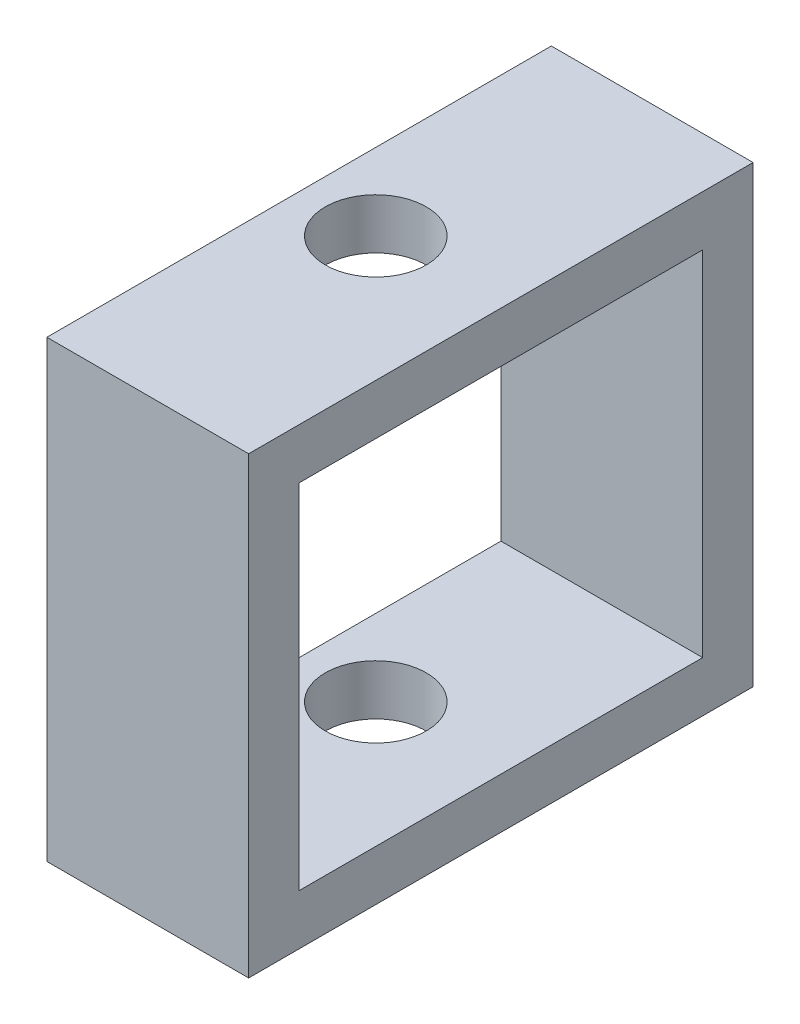
SolidWorks part; units mm, degrees
material "6061-T6 (SS)"
ref_plane "Front Plane" through (0, 0, 0) normal (0, 0, 1) x (1, 0, 0)
ref_plane "Top Plane" through (0, 0, 0) normal (0, 1, 0) x (1, 0, 0)
ref_plane "Right Plane" through (0, 0, 0) normal (1, 0, 0) x (0, 0, -1)
sketch "Sketch1" plane through (0, 0, 0) normal (0, 1, 0) x (1, 0, 0)
  line L1 (0, 0) -> (12.7, 0)
  line L2 (0, 0) -> (0, 31.75)
  line L3 (0, 31.75) -> (12.7, 31.75)
  line L4 (12.7, 0) -> (12.7, 31.75)
  circle A0 centre (4.826, 15.875) radius 3.175
  point P9 (0, 15.875)
  dimension "D1" = 6.35
  dimension "D2" = 31.75
  dimension "D3" = 12.7
  dimension "D5" = 4.826
extrude "Boss-Extrude2" add sketch "Sketch1" along normal blind 3.175
sketch "Sketch2" plane through (0, 3.175, 0) normal (0, 1, 0) x (1, 0, 0)
  line L0 (12.7, 0) -> (12.7, 31.75) construction
  line L1 (0, 31.75) -> (12.7, 31.75)
  line L2 (0, 31.75) -> (0, 28.575)
  line L3 (0, 28.575) -> (12.7, 28.575)
  line L4 (12.7, 31.75) -> (12.7, 28.575)
  line L6 (12.7, 28.575) -> (11.684, 28.575)
  line L7 (12.7, 28.575) -> (12.7, 0)
  line L15 (0, 3.175) -> (12.7, 3.175)
  line L16 (0, 31.75) -> (0, 0) construction
  line L17 (0, 0) -> (12.7, 0) construction
  line M9 (0, 31.75) -> (0, 0)
  line M10 (0, 0) -> (12.7, 0)
  line M11 (12.7, 0) -> (12.7, 31.75)
  line M12 (12.7, 31.75) -> (0, 31.75)
  dimension "D1" = 3.175
  dimension "D3" = 3.175
extrude "Boss-Extrude4" add sketch "Sketch2" along normal blind 22.225 contours L3 M9 M11 M12 | L15 M9 M10 M11
sketch "Sketch3" plane through (0, 25.4, 0) normal (0, 1, 0) x (1, 0, 0)
  line L0 (12.7, 28.575) -> (12.7, 31.75) construction
  line L1 (12.7, 3.175) -> (12.7, 28.575) construction
  line L2 (12.7, 0) -> (12.7, 3.175) construction
  line L3 (0, 0) -> (12.7, 0) construction
  line L4 (0, 3.175) -> (0, 0) construction
  line L5 (0, 31.75) -> (0, 28.575) construction
  line L6 (0, 28.575) -> (0, 3.175) construction
  line L7 (12.7, 31.75) -> (0, 31.75) construction
  line L8 (12.7, 28.575) -> (12.7, 31.75)
  line L9 (12.7, 3.175) -> (12.7, 28.575)
  line L10 (12.7, 0) -> (12.7, 3.175)
  line L11 (0, 0) -> (12.7, 0)
  line L12 (0, 3.175) -> (0, 0)
  line L13 (0, 31.75) -> (0, 28.575)
  line L14 (0, 28.575) -> (0, 3.175)
  line L15 (12.7, 31.75) -> (0, 31.75)
  circle A1 centre (4.826, 15.875) radius 3.175
  point P1 (0, 15.875)
extrude "Boss-Extrude5" add sketch "Sketch3" along normal blind 3.175
